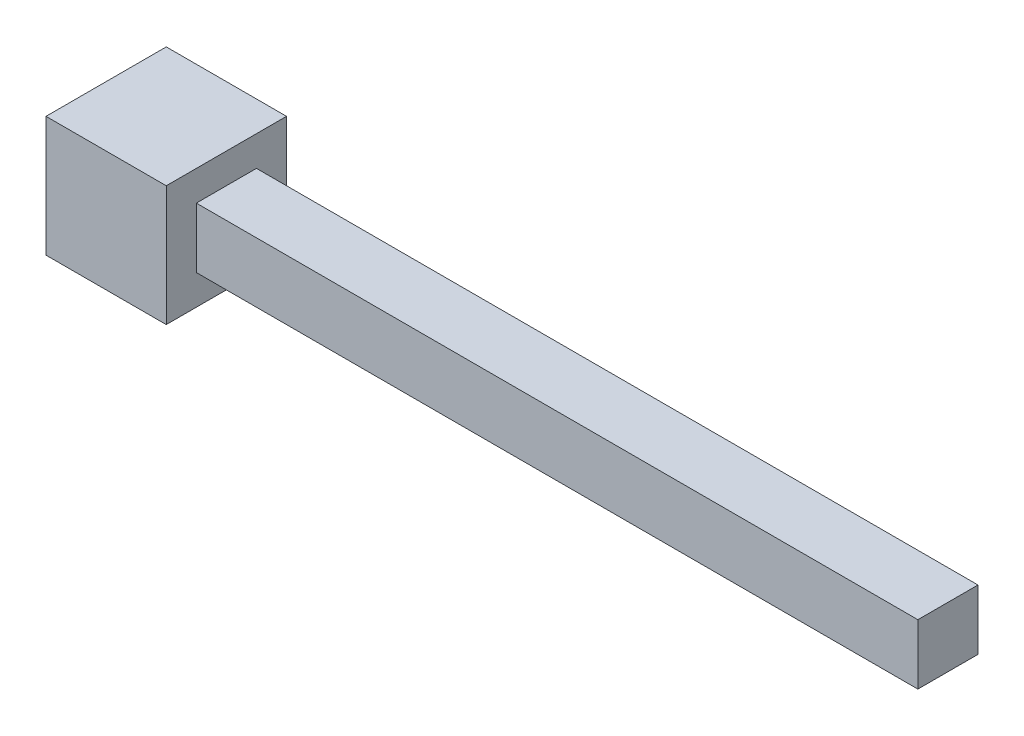
SolidWorks part; units mm, degrees
ref_plane "Front Plane" through (0, 0, 0) normal (0, 0, 1) x (1, 0, 0)
ref_plane "Top Plane" through (0, 0, 0) normal (0, 1, 0) x (1, 0, 0)
ref_plane "Right Plane" through (0, 0, 0) normal (1, 0, 0) x (0, 0, -1)
sketch "Sketch4" plane through (0, 0, 0) normal (0, 0, 1) x (1, 0, 0)
  line L5 (-63.5, -11.0963) -> (-38.1, -11.0963)
  line L6 (-63.5, -11.0963) -> (-63.5, 14.3037)
  line L11 (-63.5, 14.3037) -> (-38.1, 14.3037)
  line L12 (-38.1, -11.0963) -> (-38.1, 14.3037)
  line L13 (-63.5, -11.0963) -> (-38.1, 14.3037) construction
  line L14 (-63.5, 14.3037) -> (-38.1, -11.0963) construction
  point P0 (-50.8, 1.6037)
  dimension "D1" = 25.4
  dimension "D2" = 25.4
  dimension "D3" = 38.1
extrude "Boss-Extrude1" add sketch "Sketch4" along normal blind 25.4
sketch "Sketch5" plane through (-38.1, 0, 0) normal (1, 0, 0) x (0, 0, -1)
  line L0 (-25.4, -11.0963) -> (-25.4, 14.3037) construction
  line L1 (-19.05, -4.7463) -> (-6.35, -4.7463)
  line L2 (-19.05, -4.7463) -> (-19.05, 7.9537)
  line L3 (-19.05, 7.9537) -> (-6.35, 7.9537)
  line L4 (-6.35, -4.7463) -> (-6.35, 7.9537)
  line L5 (-19.05, -4.7463) -> (-6.35, 7.9537) construction
  line L6 (-19.05, 7.9537) -> (-6.35, -4.7463) construction
  line L7 (-25.4, 14.3037) -> (0, 14.3037) construction
  point P0 (-12.7, 1.6037)
  dimension "D1" = 12.7
  dimension "D2" = 12.7
  dimension "D3" = 12.7
  dimension "D4" = 12.7
extrude "Boss-Extrude2" add sketch "Sketch5" along normal blind 152.4
ref_plane "Plane1" through (0, 0, 12.7) normal (0, 0, 1) x (1, 0, 0)
